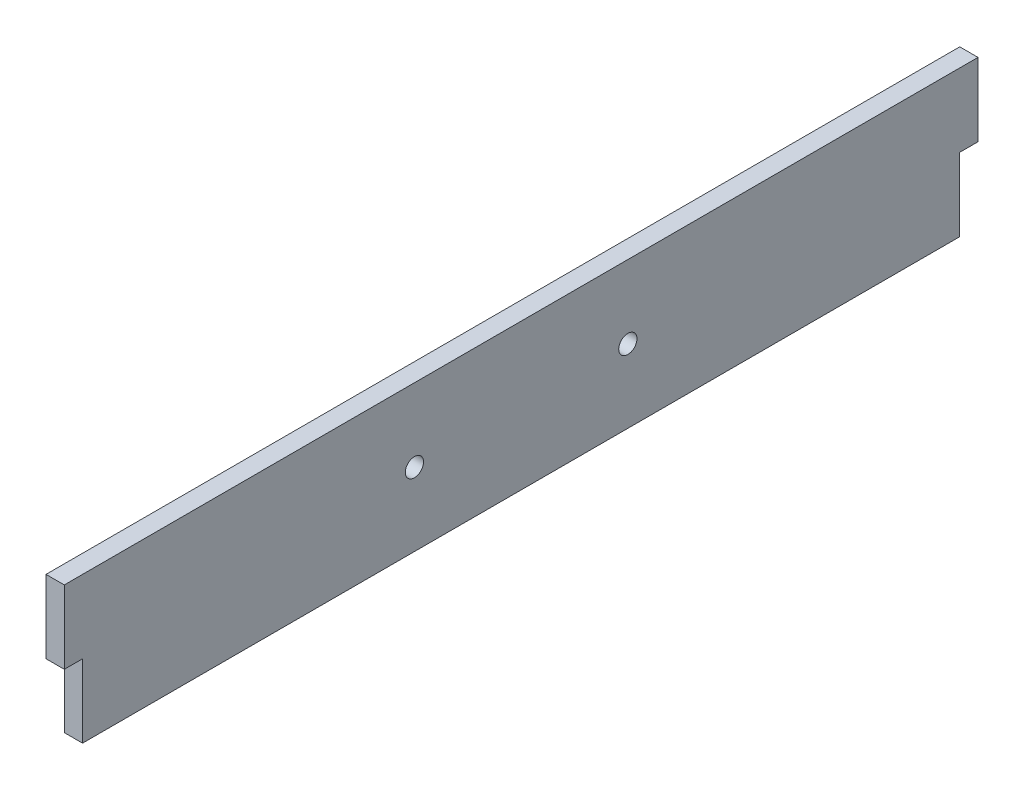
SolidWorks part; units mm, degrees
ref_plane "Front" through (0, 0, 0) normal (0, 0, 1) x (1, 0, 0)
ref_plane "Top" through (0, 0, 0) normal (0, 1, 0) x (1, 0, 0)
ref_plane "Right" through (0, 0, 0) normal (1, 0, 0) x (0, 0, -1)
sketch "Sketch1" plane through (0, 0, 0) normal (1, 0, 0) x (0, 0, -1)
  line L1 (0, 0) -> (158.75, 0)
  line L2 (0, 0) -> (0, 25.4)
  line L3 (0, 25.4) -> (158.75, 25.4)
  line L4 (158.75, 0) -> (158.75, 25.4)
  dimension "D1" = 158.75
  dimension "D2" = 25.4
extrude "Boss-Extrude1" add sketch "Sketch1" along normal blind 3.175
sketch "Sketch2" plane through (0, 0, 0) normal (-1, 0, 0) x (0, 0, 1)
  line L0 (-79.375, 25.4) -> (-79.375, 0) construction
  line L1 (-158.75, 25.4) -> (0, 25.4) construction
  line L2 (0, 0) -> (-158.75, 0) construction
  line L3 (0, 12.7) -> (-3.175, 12.7)
  line L4 (-158.75, 0) -> (-155.575, 0)
  line L5 (-158.75, 0) -> (-158.75, 12.7)
  line L6 (-158.75, 12.7) -> (-155.575, 12.7)
  line L7 (-155.575, 0) -> (-155.575, 12.7)
  line L8 (-3.175, 0) -> (-3.175, 12.7)
  line L9 (0, 0) -> (-3.175, 0)
  line L10 (0, 0) -> (0, 12.7)
  line L11 (-158.75, 12.7) -> (0, 12.7) construction
  circle A0 centre (-97.917, 12.7) radius 1.5875
  circle A1 centre (-60.833, 12.7) radius 1.5875
  dimension "D3" = 3.175
  dimension "D1" = 3.175
  dimension "D2" = 12.7
  dimension "D4" = 18.542
extrude "Cut-Extrude1" cut sketch "Sketch2" against normal through all
